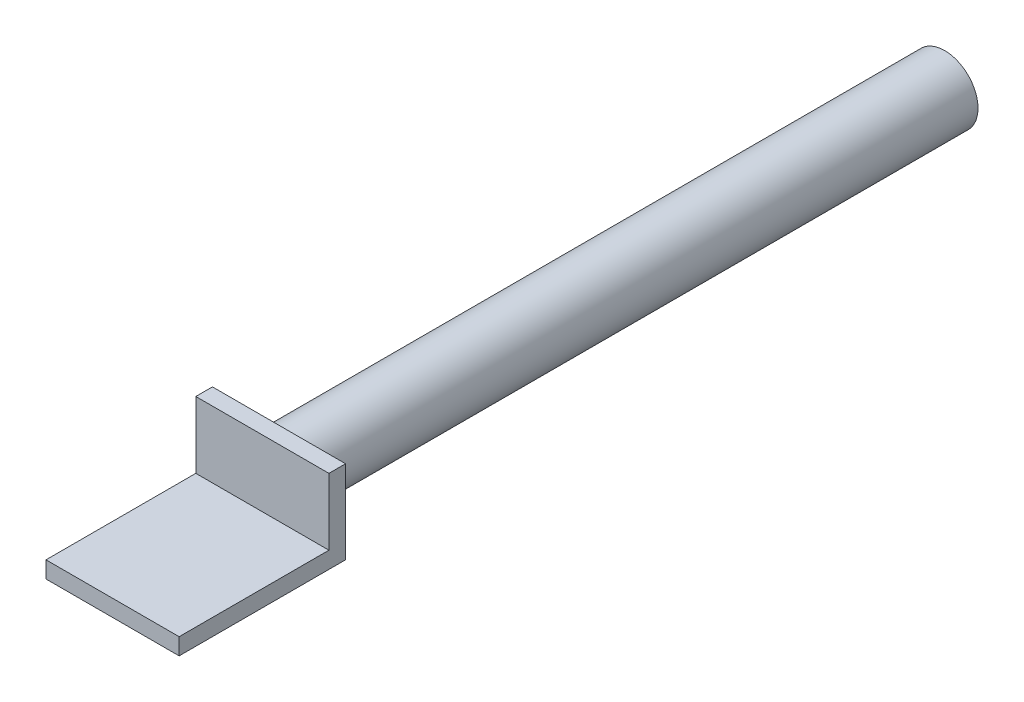
SolidWorks part; units mm, degrees
ref_plane "Front Plane" through (0, 0, 0) normal (0, 0, 1) x (1, 0, 0)
ref_plane "Top Plane" through (0, 0, 0) normal (0, 1, 0) x (1, 0, 0)
ref_plane "Right Plane" through (0, 0, 0) normal (1, 0, 0) x (0, 0, -1)
sketch "Sketch1" plane through (0, 0, 0) normal (0, 0, 1) x (1, 0, 0)
  circle A0 centre (0, 0) radius 12.7
  dimension "D1" = 25.4
extrude "Boss-Extrude1" add sketch "Sketch1" along normal blind 254
sketch "Sketch2" plane through (0, 0, 254) normal (0, 0, 1) x (1, 0, 0)
  line L1 (-25.4, 15.875) -> (25.4, 15.875)
  line L2 (-25.4, 15.875) -> (-25.4, -15.875)
  line L3 (-25.4, -15.875) -> (25.4, -15.875)
  line L4 (25.4, 15.875) -> (25.4, -15.875)
  line L5 (-25.4, 15.875) -> (25.4, -15.875) construction
  line L6 (-25.4, -15.875) -> (25.4, 15.875) construction
  point P0 (0, 0)
  dimension "D1" = 50.8
  dimension "D2" = 31.75
extrude "Boss-Extrude2" add sketch "Sketch2" along normal blind 63.5
sketch "Sketch3" plane through (25.4, 0, 0) normal (1, 0, 0) x (0, 0, -1)
  line L1 (-317.5, 15.875) -> (-260.35, 15.875)
  line L2 (-317.5, 15.875) -> (-317.5, -9.525)
  line L3 (-317.5, -9.525) -> (-260.35, -9.525)
  line L4 (-260.35, 15.875) -> (-260.35, -9.525)
  dimension "D1" = 57.15
  dimension "D2" = 25.4
extrude "Cut-Extrude1" cut sketch "Sketch3" against normal up to next
